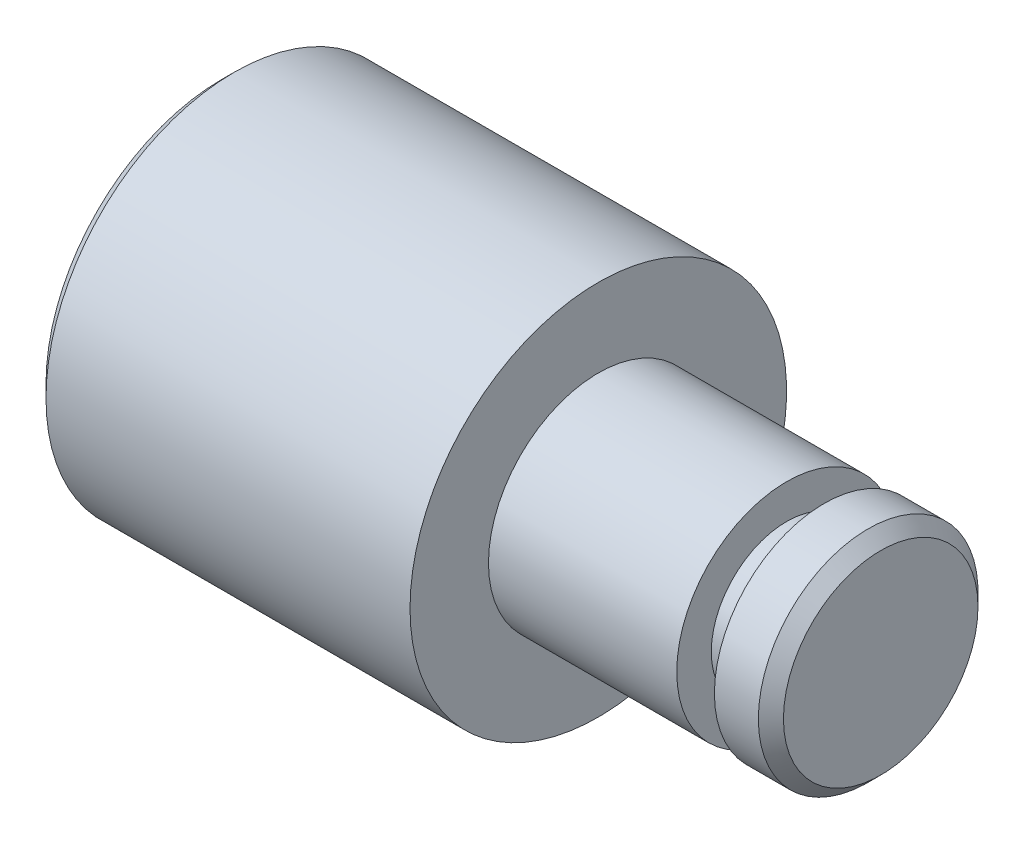
SolidWorks part; units mm, degrees
ref_plane "Plan de face" through (0, 0, 0) normal (0, 0, 1) x (1, 0, 0)
ref_plane "Plan de dessus" through (0, 0, 0) normal (0, 1, 0) x (1, 0, 0)
ref_plane "Plan de droite" through (0, 0, 0) normal (1, 0, 0) x (0, 0, -1)
sketch "Esquisse1" plane through (0, 0, 0) normal (0, 0, 1) x (1, 0, 0)
  line L0 (0, 0) -> (22.9545, 0) construction
  line L1 (0, 0) -> (0, 1.75)
  line L2 (0, 1.75) -> (-0.9, 1.75)
  line L4 (-1.5, 1.75) -> (-4.5, 1.75)
  line L5 (-4.5, 1.75) -> (-4.5, 3)
  line L6 (-4.5, 3) -> (-10.5, 3)
  line L7 (-10.5, 3) -> (-10.5, 0)
  line L8 (-10.5, 0) -> (0, 0)
  line L9 (-0.9, 1.75) -> (-0.9, 1.2)
  line L10 (-0.9, 1.2) -> (-1.5, 1.2)
  line L11 (-1.5, 1.2) -> (-1.5, 1.75)
  dimension "D1" = 2.4
  dimension "D2" = 6
  dimension "D3" = 3.5
  dimension "D4" = 0.6
  dimension "D5" = 10.5
  dimension "D6" = 6
  dimension "D7" = 9
revolve "Révolution1" add sketch "Esquisse1" angle 360 about L0
chamfer "Chanfrein1" distance 0.2 angle 45 2 edges at (0, 0, 1.75) (-10.5, 0, 3)
